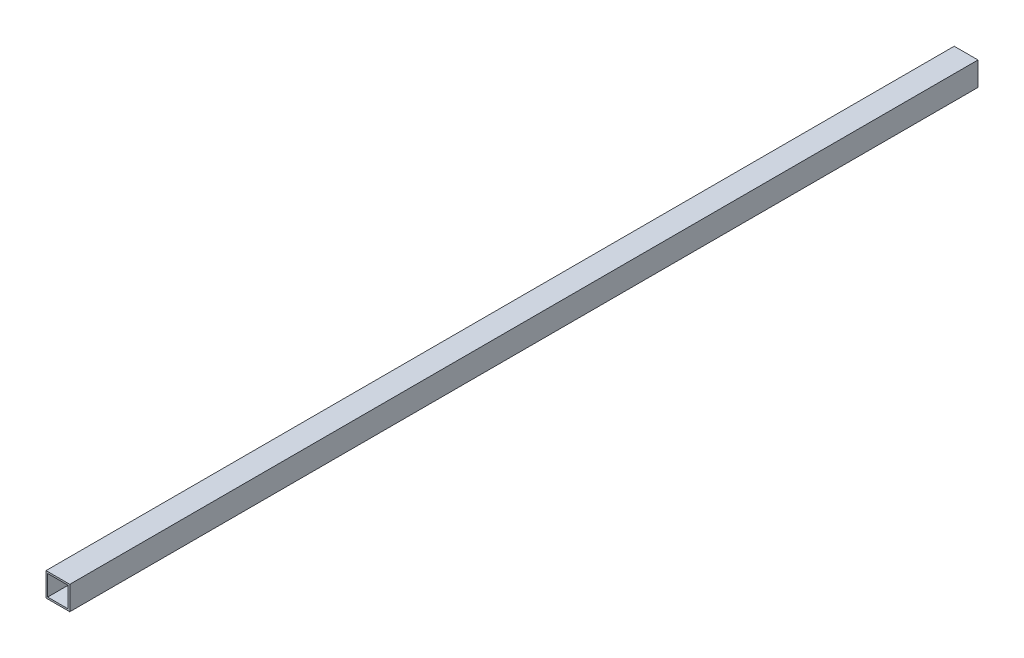
SolidWorks part; units mm, degrees
material "6061 Alloy"
ref_plane "Front Plane" through (0, 0, 0) normal (0, 0, 1) x (1, 0, 0)
ref_plane "Top Plane" through (0, 0, 0) normal (0, 1, 0) x (1, 0, 0)
ref_plane "Right Plane" through (0, 0, 0) normal (1, 0, 0) x (0, 0, -1)
sketch "Sketch1" plane through (0, 0, 0) normal (0, 0, 1) x (1, 0, 0)
  line L0 (-7.3, 7.3) -> (7.3, 7.3)
  line L1 (-8.5, -8.5) -> (8.5, -8.5)
  line L2 (-8.5, -8.5) -> (-8.5, 8.5)
  line L3 (-8.5, 8.5) -> (8.5, 8.5)
  line L4 (8.5, -8.5) -> (8.5, 8.5)
  line L5 (-8.5, -8.5) -> (8.5, 8.5) construction
  line L6 (-8.5, 8.5) -> (8.5, -8.5) construction
  line L7 (7.3, -7.3) -> (7.3, 7.3)
  line L8 (-7.3, -7.3) -> (7.3, -7.3)
  line L9 (-7.3, -7.3) -> (-7.3, 7.3)
  point P0 (0, 0)
  dimension "D1" = 17
  dimension "D2" = 17
  dimension "D3" = 1.2
extrude "Boss-Extrude1" add sketch "Sketch1" along normal blind 649
